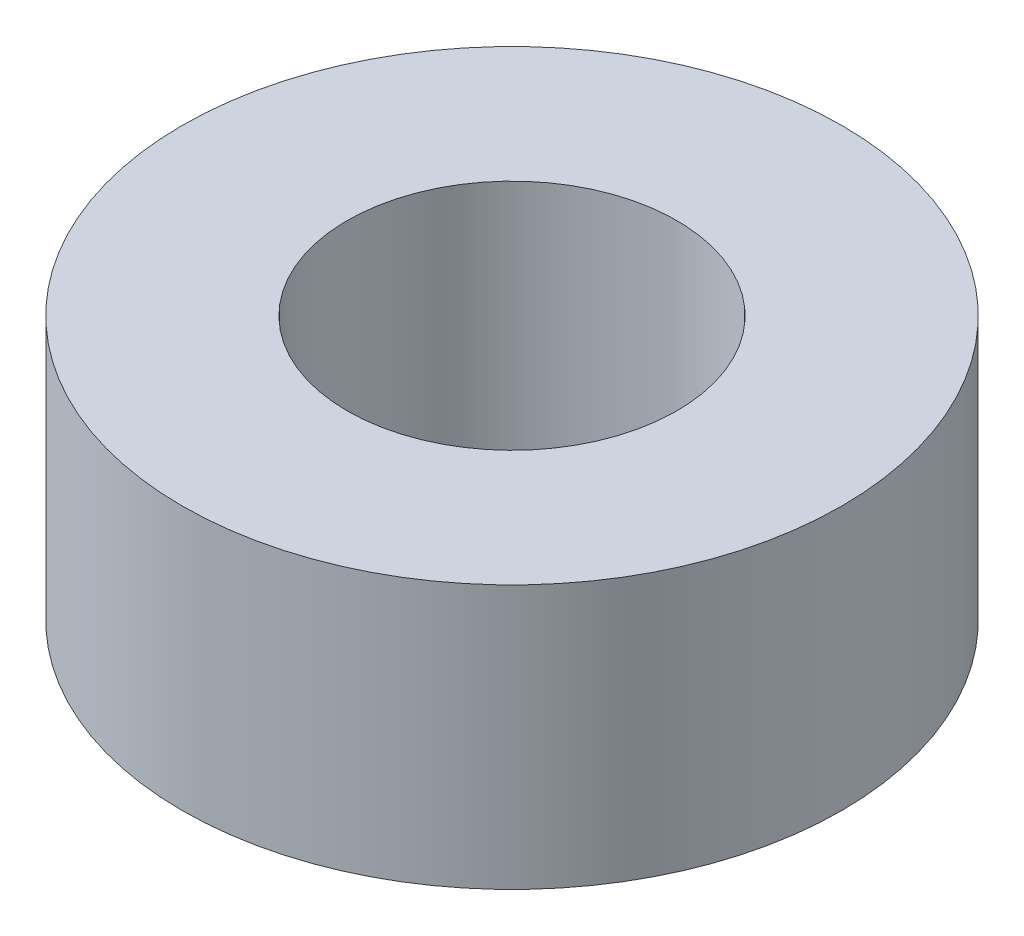
SolidWorks part; units mm, degrees
ref_plane "Front Plane" through (0, 0, 0) normal (0, 0, 1) x (1, 0, 0)
ref_plane "Top Plane" through (0, 0, 0) normal (0, 1, 0) x (1, 0, 0)
ref_plane "Right Plane" through (0, 0, 0) normal (1, 0, 0) x (0, 0, -1)
sketch "Sketch2" plane through (0, 0, 0) normal (0, 1, 0) x (1, 0, 0)
  circle A0 centre (0, 0) radius 5
  circle A1 centre (0, 0) radius 2.5
  dimension "D1" = 10
  dimension "D2" = 5
extrude "Boss-Extrude1" add sketch "Sketch2" along normal blind 4
